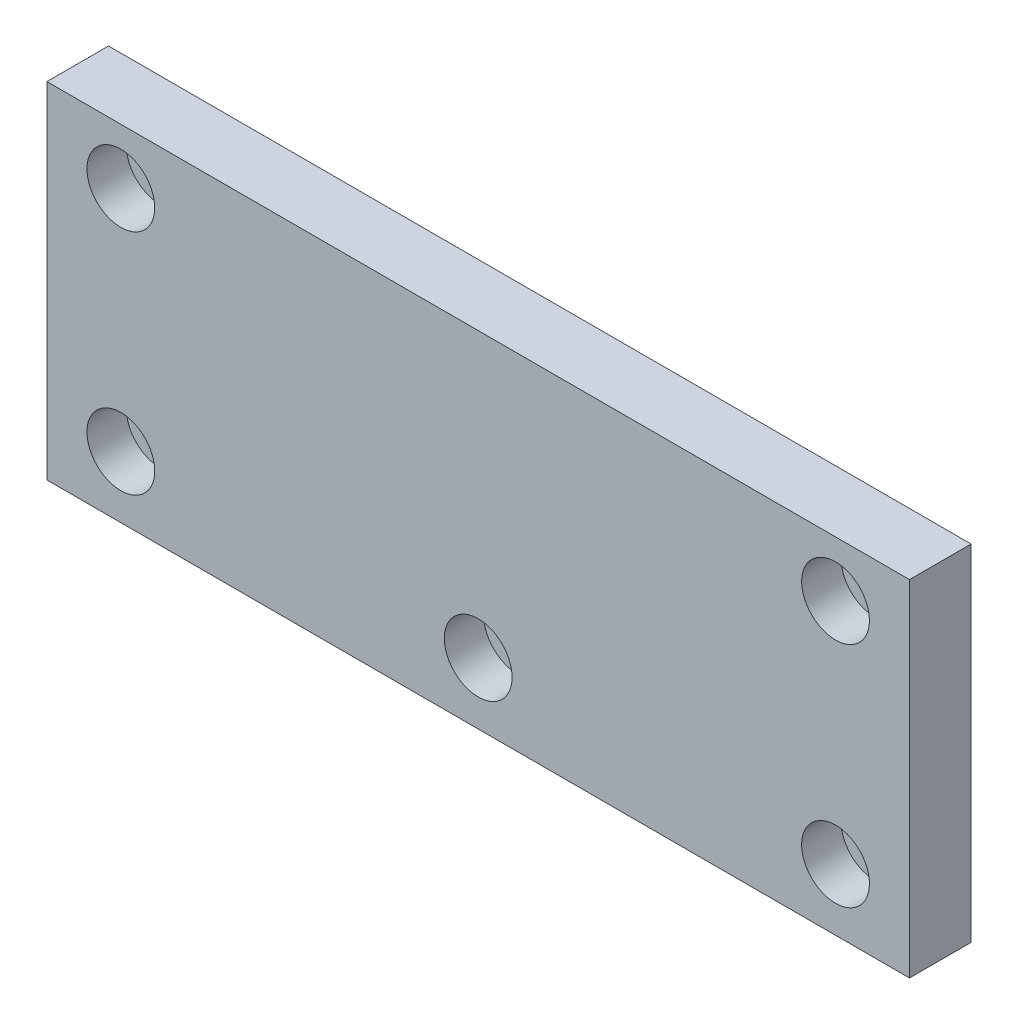
SolidWorks part; units mm, degrees
material "1023 Листовая углеродистая сталь (SS)"
ref_plane "Front" through (0, 0, 0) normal (0, 0, 1) x (1, 0, 0)
ref_plane "Top" through (0, 0, 0) normal (0, 1, 0) x (1, 0, 0)
ref_plane "Right" through (0, 0, 0) normal (1, 0, 0) x (0, 0, -1)
sketch "Sketch1" plane through (0, 0, 0) normal (0, 0, 1) x (1, 0, 0)
  line L1 (-70, 28) -> (70, 28)
  line L2 (-70, 28) -> (-70, -28)
  line L3 (-70, -28) -> (70, -28)
  line L4 (70, 28) -> (70, -28)
  line L5 (-70, 28) -> (70, -28) construction
  line L6 (-70, -28) -> (70, 28) construction
  point P0 (0, 0)
  dimension "D1" = 56
  dimension "D2" = 140
extrude "Extrude1" add sketch "Sketch1" along normal blind 10
hole_wizard "CBORE for M6 Hex Socket Head Cap Screw1" positions "Sketch2" profile "Sketch3" counterbore size "M6" standard "DIN" end condition through all
sketch "Sketch2" plane through (0, 0, 10) normal (0, 0, 1) x (1, 0, 0)
  point P0 (58, -18)
  point P3 (58, 19)
  point P6 (0, -18)
  point P9 (-58, -18)
  point P12 (-58, 19)
sketch "Sketch3" plane through (58, -18, 10) normal (1, 0, 0) x (0, -1, 0)
  line L0 (0, 0) -> (0, 10)
  line L1 (0, 10) -> (3.3, 10)
  line L3 (3.3, 10) -> (3.3, 6.4)
  line L4 (3.3, 6.4) -> (5.5, 6.4)
  line L5 (5.5, 6.4) -> (5.5, 0)
  line L7 (5.5, 0) -> (0, 0)
  line L11 (0, -6.35) -> (0, 107.95) construction
  dimension "Диаметр сквозного отверстия" = 6.6
  dimension "Глубина сквозного отверстия" = 10
  dimension "Диаметр цековки" = 11
  dimension "Глубина цековки" = 6.4
